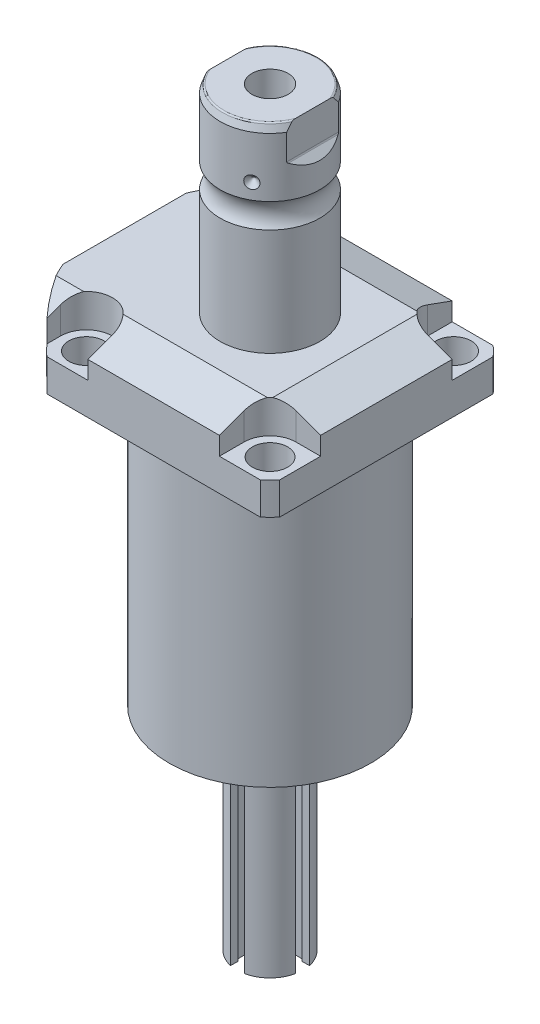
SolidWorks part; units mm, degrees
material "Alloy Steel"
ref_plane "Front Plane" through (0, 0, 0) normal (0, 0, 1) x (1, 0, 0)
ref_plane "Top Plane" through (0, 0, 0) normal (0, 1, 0) x (1, 0, 0)
ref_plane "Right Plane" through (0, 0, 0) normal (1, 0, 0) x (0, 0, -1)
ref_plane "Plane1" through (0, 0, 0) normal (0, 1, 0) x (0, 0, 1)
sketch "Sketch1" plane through (0, 0, 0) normal (0, 1, 0) x (0, 0, 1)
  line L0 (-44.45, 44.45) -> (44.45, 44.45)
  line L1 (44.45, 44.45) -> (44.45, -55.5498)
  line L2 (44.45, -55.5498) -> (-44.45, -55.5498)
  line L3 (-44.45, -55.5498) -> (-44.45, 44.45)
  line L4 (0, 0) -> (0, -60.6467) construction
  dimension "D1" = 55.5498
  dimension "D2" = 99.9998
  dimension "D3" = 88.9
extrude "Extrude1" add sketch "Sketch1" along normal blind 129.794
sketch "Sketch2" plane through (0, 0, 0) normal (0, -1, 0) x (1, 0, 0)
  circle A0 centre (0, 0) radius 60.325
  dimension "D1" = 120.65
extrude "Cut-Extrude1" cut sketch "Sketch2" against normal through all flip side to cut
ref_plane "Plane2" through (0, 0, 0) normal (1, 0, 0) x (0, 0, 1)
sketch "Sketch3" plane through (0, 0, 0) normal (1, 0, 0) x (0, 0, 1)
  line L0 (38.4937, 0) -> (38.4937, -104.775)
  line L1 (38.4937, -104.775) -> (76.5937, -104.775)
  line L2 (76.5937, -104.775) -> (76.5937, 0)
  line L3 (76.5937, 0) -> (38.4937, 0)
  line L4 (0, -93.345) -> (0, 4.445) construction
  line L5 (40.7836, 0) -> (-40.7836, 0) construction
  dimension "D1" = 76.9874
  dimension "D2" = 153.1874
  dimension "D3" = 104.775
revolve "Cut-Revolve1" cut sketch "Sketch3" angle 360 about L4
fillet "Fillet1" radius 0.381 1 edges at (0, 104.775, 38.4937)
sketch "Sketch4" plane through (0, 129.794, 0) normal (0, 1, 0) x (-1, 0, 0)
  line L0 (-44.45, 40.7836) -> (-44.45, -40.7836) construction
  line L1 (40.7836, 44.45) -> (-40.7836, 44.45) construction
  line L2 (-25.1206, -44.45) -> (-25.1206, -35.052)
  line L3 (-44.45, -44.45) -> (-25.1206, -44.45)
  line L4 (-44.45, -25.1206) -> (-44.45, -44.45)
  line L5 (-35.052, -25.1206) -> (-44.45, -25.1206)
  line L6 (44.9834, -44.45) -> (25.1206, -44.45)
  line L7 (25.1206, 44.45) -> (25.1206, 35.052)
  line L8 (44.9834, 44.45) -> (44.9834, 35.052)
  line L9 (44.9834, 44.45) -> (25.1206, 44.45)
  line L10 (-35.052, 25.1206) -> (-44.45, 25.1206)
  line L11 (-44.45, 25.1206) -> (-44.45, 44.45)
  line L12 (-44.45, 44.45) -> (-25.1206, 44.45)
  line L13 (-25.1206, 44.45) -> (-25.1206, 35.052)
  line L14 (-48.9217, 0) -> (49.4551, 0) construction
  line L15 (44.9834, -44.45) -> (44.9834, -35.052)
  line L16 (25.1206, -44.45) -> (25.1206, -35.052)
  arc A0 (25.1206, -35.052) -> (44.9834, -35.052) centre (35.052, -35.052) cw
  arc A1 (-35.052, -25.1206) -> (-25.1206, -35.052) centre (-35.052, -35.052) cw
  arc A2 (-35.052, 25.1206) -> (-25.1206, 35.052) centre (-35.052, 35.052) ccw
  arc A3 (25.1206, 35.052) -> (44.9834, 35.052) centre (35.052, 35.052) ccw
  dimension "D2" = 9.9314
  dimension "D1" = 35.052
  dimension "D3" = 35.052
  dimension "D4" = 35.052
extrude "Cut-Extrude2" cut sketch "Sketch4" against normal blind 12.7
ref_plane "Plane3" through (0, 0, 0) normal (1, 0, 0) x (0, 0, -1)
sketch "Sketch5" plane through (0, 0, 0) normal (1, 0, 0) x (0, 0, -1)
  line L0 (-28.575, 129.794) -> (-44.45, 124.016)
  line L1 (0, 0) -> (0, 154.1081) construction
  line L2 (-28.575, 129.794) -> (-44.45, 129.794)
  line L3 (-44.45, 129.794) -> (-44.45, 124.016)
  dimension "D1" = 15.875
  dimension "D2" = 20
extrude "Cut-Extrude9" cut sketch "Sketch5" against normal through all and the other way through all
mirror "Mirror1" about plane through (0, 0, 0) normal (0, 0, 1) of "Cut-Extrude9"
ref_plane "Plane7" through (0, 0, 0) normal (0, 0, 1) x (1, 0, 0)
sketch "Sketch9" plane through (0, 0, 0) normal (0, 0, 1) x (1, 0, 0)
  line L0 (28.575, 129.794) -> (44.45, 124.016)
  line L1 (44.45, 124.016) -> (44.45, 129.794)
  line L2 (44.45, 129.794) -> (28.575, 129.794)
  dimension "D1" = 15.875
  dimension "D2" = 20
extrude "Cut-Extrude7" cut sketch "Sketch9" against normal through all and the other way through all
ref_plane "Plane8" through (-41.402, 88.9, -18.1102) normal (1, 0, 0) x (0, 1, 0)
sketch "Sketch20" plane through (-41.402, 88.9, -18.1102) normal (1, 0, 0) x (0, 1, 0)
  line L0 (-88.9, 18.1102) -> (39.8401, 18.1102) construction
  line L1 (-7.2797, 36.2204) -> (36.9042, 36.2204) construction
  line L2 (15.875, 41.9227) -> (17.3228, 41.9227)
  line L3 (15.875, 58.8938) -> (15.875, -22.6734) construction
  line L4 (17.3228, 41.9227) -> (17.3228, 39.4716)
  line L5 (17.3228, 39.4716) -> (18.3388, 39.4716)
  line L6 (18.3388, 39.4716) -> (18.3388, 37.465)
  line L7 (18.3388, 37.465) -> (29.3116, 37.465)
  line L8 (29.3116, 37.465) -> (29.3116, 36.2204)
  line L9 (29.3116, 36.2204) -> (15.875, 36.2204)
  line L10 (15.875, 41.9227) -> (15.875, 36.2204)
  dimension "D1" = 18.1102
  dimension "D2" = 11.4046
  dimension "D3" = 1.4478
  dimension "D4" = 6.5024
  dimension "D5" = 1.016
  dimension "D6" = 2.4892
  dimension "D7" = 10.9728
revolve "Cut-Revolve4" cut sketch "Sketch20" angle 360 about L1
mirror "Mirror10" about plane through (0, 0, 0) normal (0, 0, 1) of "Cut-Revolve4"
sketch "Sketch10" plane through (-41.402, 88.9, -18.1102) normal (1, 0, 0) x (0, 1, 0)
  line L0 (-1.0325, 0) -> (1.5659, 0) construction
  line L1 (29.3116, 1.2446) -> (18.3388, 1.2446) construction
  line L2 (18.3388, -1.2446) -> (29.3116, -1.2446) construction
  line L3 (15.875, 58.8938) -> (15.875, -22.6734) construction
  circle A0 centre (16.1417, 4.5212) radius 1.1811
  dimension "D1" = 2.3622
  dimension "D2" = 0.2667
  dimension "D3" = 9.0424
revolve "Revolve4" add sketch "Sketch10" angle 360 about L0
ref_plane "Plane9" through (-41.402, 88.9, 18.1102) normal (1, 0, 0) x (0, 1, 0)
sketch "Sketch11" plane through (-41.402, 88.9, 18.1102) normal (1, 0, 0) x (0, 1, 0)
  line L0 (-1.0325, 0) -> (1.5659, 0) construction
  line L1 (29.3116, 1.2446) -> (18.3388, 1.2446) construction
  line L3 (15.875, 22.6734) -> (15.875, -58.8938) construction
  line L4 (18.3388, -1.2446) -> (29.3116, -1.2446) construction
  circle A0 centre (16.1417, 4.5212) radius 1.1811
  dimension "D1" = 2.3622
  dimension "D2" = 9.0424
  dimension "D3" = 0.2667
revolve "Revolve2" add sketch "Sketch11" angle 360 about L0
ref_plane "Plane10" through (-55.5498, 101.9048, 12.9794) normal (0, 0, 1) x (0, 1, 0)
sketch "S2D0007" plane through (-55.5498, 101.9048, 12.9794) normal (0, 0, 1) x (0, 1, 0)
  line L0 (15.875, 0) -> (26.3525, 0)
  line L1 (26.3525, 0) -> (26.3525, -0.254)
  line L2 (26.3525, -0.254) -> (22.0599, -0.254)
  line L3 (22.0599, -0.254) -> (21.5173, -2.8067)
  line L4 (21.5173, -2.8067) -> (20.8534, -3.4706)
  line L5 (20.8534, -3.4706) -> (20.8534, -14.224)
  line L6 (20.8534, -14.224) -> (15.875, -14.224)
  line L7 (15.875, -14.224) -> (15.875, 0)
  line L8 (15.875, -1000) -> (15.875, 49000) construction
  line L9 (2.8702, 0) -> (2.8702, -14.7662) construction
  dimension "D1" = 0.254
  dimension "D2" = 13.0048
  dimension "D3" = 9.9568
  dimension "D4" = 20.955
  dimension "D5" = 12.3698
  dimension "D6" = 12
  dimension "D7" = 45
  dimension "D8" = 13.97
  dimension "D9" = 2.5527
revolve "Cut-Revolve2" cut sketch "S2D0007" angle 360 about L8
ref_plane "Plane11" through (-55.5498, 101.9048, -12.9794) normal (0, 0, 1) x (0, 1, 0)
sketch "Sketch13" plane through (-55.5498, 101.9048, -12.9794) normal (0, 0, 1) x (0, 1, 0)
  line L0 (15.875, 0) -> (26.3525, 0)
  line L1 (26.3525, 0) -> (26.3525, -0.254)
  line L2 (26.3525, -0.254) -> (22.0599, -0.254)
  line L3 (22.0599, -0.254) -> (21.5173, -2.8067)
  line L4 (21.5173, -2.8067) -> (20.8534, -3.4706)
  line L5 (20.8534, -3.4706) -> (20.8534, -14.224)
  line L6 (20.8534, -14.224) -> (15.875, -14.224)
  line L7 (15.875, -14.224) -> (15.875, 0)
  line L8 (15.875, -1000) -> (15.875, 49000) construction
  line L9 (2.8702, 0) -> (2.8702, -14.7662) construction
  dimension "D1" = 0.254
  dimension "D2" = 13.0048
  dimension "D3" = 20.955
  dimension "D4" = 12.3698
  dimension "D5" = 12
  dimension "D6" = 45
  dimension "D7" = 2.5527
  dimension "D8" = 13.97
  dimension "D9" = 9.9568
revolve "Cut-Revolve3" cut sketch "Sketch13" angle 360 about L8
ref_plane "Plane12" through (0, 0, 0) normal (1, 0, 0) x (0, -1, 0)
sketch "Sketch15" plane through (0, 0, 0) normal (1, 0, 0) x (0, -1, 0)
  line L0 (-129.794, 0) -> (-129.794, 19.05)
  line L1 (-129.794, 19.05) -> (-170.5783, 19.05)
  line L2 (-179.9925, 19.05) -> (-202.5396, 19.05)
  line L3 (-205.4606, 17.9868) -> (-205.4606, 0)
  line L4 (-205.4606, 0) -> (-129.794, 0)
  line L5 (-197.6361, 0) -> (-64.6704, 0) construction
  line L6 (-129.794, 27.5233) -> (-129.794, -27.5233) construction
  line L7 (-104.775, 40.7836) -> (-104.775, 44.45) construction
  line L8 (-205.4606, 17.9868) -> (-202.5396, 19.05)
  arc A0 (-179.9925, 19.05) -> (-170.5783, 19.05) centre (-175.2854, 25.4254) ccw
  dimension "D2" = 20
  dimension "D4" = 7.9248
  dimension "D6" = 35.0012
  dimension "D1" = 100.6856
  dimension "D3" = 38.1
  dimension "D5" = 30.1752
  dimension "D7" = 2.921
revolve "Revolve3" add sketch "Sketch15" angle 360 about L5
ref_plane "Plane13" through (0, 0, 0) normal (0, 0, -1) x (0, -1, 0)
sketch "Sketch16" plane through (0, 0, 0) normal (0, 0, -1) x (0, -1, 0)
  line L0 (-205.4606, 19.05) -> (-189.6764, 19.05)
  line L1 (-205.4606, -19.05) -> (-205.4606, -16.2814)
  line L2 (-205.4606, 16.2814) -> (-192.7606, 16.2814)
  line L3 (-192.2218, 16.5046) -> (-189.6764, 19.05)
  line L4 (-192.2218, -16.5046) -> (-189.6764, -19.05)
  line L5 (-205.4606, -16.2814) -> (-192.7606, -16.2814)
  line L6 (-205.4606, 19.05) -> (-205.4606, 16.2814)
  line L7 (-205.4606, -19.05) -> (-189.6764, -19.05)
  line L8 (-194.0458, 0) -> (-125.0021, 0) construction
  line L11 (-205.4606, 17.9868) -> (-205.4606, -17.9868) construction
  line L12 (-179.9925, 19.05) -> (-202.5396, 19.05) construction
  arc A0 (-192.7606, 16.2814) -> (-192.2218, 16.5046) centre (-192.7606, 17.0434) ccw
  arc A1 (-192.7606, -16.2814) -> (-192.2218, -16.5046) centre (-192.7606, -17.0434) cw
  point P3 (-192.445, 16.2814)
  dimension "D4" = 0.762
  dimension "D1" = 32.5628
  dimension "D2" = 45
  dimension "D3" = 12.7
extrude "Cut-Extrude8" cut sketch "Sketch16" against normal mid plane 106.68
hole_wizard "Hole1" positions "Sketch18" profile "Sketch17" legacy end condition up to next
sketch "Sketch18" plane through (0, 117.094, 0) normal (0, 1, 0) x (-1, 0, 0)
  arc A0 (44.9834, -35.052) -> (25.1206, -35.052) centre (35.052, -35.052) ccw construction
  arc A1 (25.1206, 35.052) -> (44.9834, 35.052) centre (35.052, 35.052) ccw construction
  arc A2 (-35.052, 25.1206) -> (-25.1206, 35.052) centre (-35.052, 35.052) ccw construction
  arc A3 (-25.1206, -35.052) -> (-35.052, -25.1206) centre (-35.052, -35.052) ccw construction
  point P0 (-35.052, -35.052)
  point P1 (-35.052, 35.052)
  point P3 (35.052, 35.052)
  point P5 (35.052, -35.052)
sketch "Sketch17" plane through (35.052, 117.094, -35.052) normal (1, 0, 0) x (0, 0, 1)
  line L0 (0, 0) -> (0, 12.319)
  line L1 (0, 12.319) -> (6.7437, 12.319)
  line L2 (6.7437, 12.319) -> (6.7437, 0)
  line L3 (6.7437, 0) -> (0, 0)
  line L4 (0, 110) -> (0, -10) construction
  dimension "Diameter" = 13.4874
  dimension "Depth" = 12.319
chamfer "Chamfer1" distance 0.635 angle 45 2 edges at (-41.402, 107.2388, 16.8656) (-41.402, 107.2388, -16.8656)
sketch "Sketch21" plane through (0, 0, 0) normal (0, 0, 1) x (1, 0, 0)
  line L0 (0, 0) -> (0, 194.0957) construction
  line L1 (0, 180.0606) -> (6.9342, 184.2271)
  line L2 (6.9342, 184.2271) -> (6.9342, 205.4606)
  line L4 (6.9342, 205.4606) -> (0, 205.4606)
  line L5 (0, 205.4606) -> (0, 180.0606)
  line L6 (16.2814, 205.4606) -> (-16.2814, 205.4606) construction
  dimension "D1" = 13.8684
  dimension "D2" = 59
  dimension "D3" = 25.4
revolve "Cut-Revolve5" cut sketch "Sketch21" angle 360 about L0
fillet "Fillet2" radius 0.635 2 edges at (0, 205.4606, 17.9868) (0, 205.4606, -17.9868)
sketch "Sketch22" plane through (0, 0, 0) normal (0, 0, 1) x (1, 0, 0)
  line L0 (-37.9974, 185.9534) -> (37.12, 185.9534) construction
  line L1 (-19.05, 188.3664) -> (-16.637, 185.9534)
  line L2 (-16.637, 185.9534) -> (-19.05, 185.9534)
  line L3 (-19.05, 185.9534) -> (-19.05, 188.3664)
  line L4 (-19.05, 189.6764) -> (-19.05, 179.9925) construction
  arc A0 (-19.05, 170.5783) -> (-19.05, 179.9925) centre (-25.4254, 175.2854) ccw construction
  dimension "D2" = 10.668
  dimension "D1" = 4.826
  dimension "D3" = 45
revolve "Cut-Revolve6" cut sketch "Sketch22" angle 360 about L0
pattern_circular "CirPattern1" count 3 over 360 about axis through (0, 197.6361, 0) along (0, 1, 0) of "Cut-Revolve6"
sketch "Sketch23" plane through (0, 0, 0) normal (0, 0, 1) x (1, 0, 0)
  line L0 (0, -1000) -> (0, 49000) construction
  line L1 (0, 0) -> (22.225, 0)
  line L2 (-38.4937, 0) -> (38.4937, 0) construction
  line L3 (22.225, 0) -> (22.225, -2.54)
  line L4 (22.225, -2.54) -> (12.7, -2.54)
  line L5 (12.7, -2.54) -> (12.7, -81.28)
  line L6 (12.7, -81.28) -> (0, -81.28)
  line L7 (0, -81.28) -> (0, 0)
  dimension "D1" = 44.45
  dimension "D2" = 25.4
  dimension "D3" = 2.54
  dimension "D4" = 81.28
revolve "Revolve5" add sketch "Sketch23" angle 360 about L0
sketch "Sketch24" plane through (0, -2.54, 0) normal (0, -1, 0) x (1, 0, 0)
  line L0 (-1000, 0) -> (49000, 0) construction
  line L1 (0, -1000) -> (0, 49000) construction
  line L2 (0, 0) -> (43301.2702, 25000) construction
  line L3 (0, 0) -> (25000, 43301.2702) construction
  circle A0 centre (0, 0) radius 19.431 construction
  circle A1 centre (19.431, 0) radius 1.7272
  circle A2 centre (16.8277, 9.7155) radius 1.7272
  circle A3 centre (9.7155, 16.8277) radius 1.7272
  circle A4 centre (0, 19.431) radius 1.7272
  circle A5 centre (-9.7155, 16.8277) radius 1.7272
  circle A6 centre (-16.8277, 9.7155) radius 1.7272
  circle A7 centre (-19.431, 0) radius 1.7272
  circle A8 centre (-16.8277, -9.7155) radius 1.7272
  circle A9 centre (-9.7155, -16.8277) radius 1.7272
  circle A10 centre (0, -19.431) radius 1.7272
  circle A11 centre (9.7155, -16.8277) radius 1.7272
  circle A12 centre (16.8277, -9.7155) radius 1.7272
  dimension "D3" = 38.862
  dimension "D4" = 3.4544
  dimension "D5" = 3.4544
  dimension "D6" = 3.4544
  dimension "D7" = 3.4544
  dimension "D1" = 30
  dimension "D2" = 30
extrude "Cut-Extrude10" cut sketch "Sketch24" against normal up to surface (2.54 mm away) up to face at (0, 0, -22.225)
sketch "Sketch25" plane through (0, -2.54, 0) normal (0, -1, 0) x (1, 0, 0)
  circle A0 centre (19.431, 0) radius 2.7051
  circle A1 centre (-9.7155, 16.8277) radius 2.7051
  circle A2 centre (-9.7155, -16.8277) radius 2.7051
  dimension "D1" = 5.4102
  dimension "D2" = 5.4102
  dimension "D3" = 5.4102
extrude "Extrude2" add sketch "Sketch25" along normal blind 2.9464
ref_plane "Plane15-slot-angle" through (0, 0, 0) normal (1, 0, 0) x (0, 0, -1)
ref_plane "Plane16" through (0, -41.91, 12.7) normal (0, 0, 1) x (-1, 0, 0)
sketch "Sketch31" plane through (0, -41.91, 12.7) normal (0, 0, 1) x (-1, 0, 0)
  line L0 (0, -1034.036) -> (0, 48965.964) construction
  line L1 (0, -1034.036) -> (0, 48965.964) construction
  line L2 (-2.6416, -28.9574) -> (-2.6416, 39.37)
  line L3 (12.7, 39.37) -> (-12.7, 39.37) construction
  line L4 (-2.6416, 39.37) -> (2.6416, 39.37)
  line L5 (2.6416, -28.9574) -> (2.6416, 39.37)
  arc A0 (-2.6416, -28.9574) -> (2.6416, -28.9574) centre (0, -31.242) ccw
  point P14 (0, 39.37)
  dimension "D1" = 6.985
  dimension "D2" = 5.2832
  dimension "D3" = 70.612
extrude "Cut-Extrude11" cut sketch "Sketch31" against normal blind 6.477
sketch "Sketch32" plane through (0, 0, 6.223) normal (0, 0, 1) x (1, 0, 0)
  line L0 (0, -1000) -> (0, 49000) construction
  line L1 (3.4925, -10.668) -> (3.4925, -81.28)
  line L2 (-12.7, -81.28) -> (12.7, -81.28) construction
  line L3 (3.4925, -81.28) -> (-3.4925, -81.28)
  line L4 (-2.6416, -81.28) -> (2.6416, -81.28) construction
  line L5 (3.4925, -10.668) -> (-3.4925, -10.668)
  line L6 (-3.4925, -10.668) -> (-3.4925, -81.28)
  point P13 (0, -81.28)
  point P14 (0, -10.668)
  dimension "D1" = 6.985
extrude "Cut-Extrude12" cut sketch "Sketch32" along normal blind 3.302
ref_plane "Plane17" through (0, 0, 0) normal (0, 0, 1) x (1, 0, 0)
mirror "Mirror11" about plane through (0, 0, 0) normal (0, 0, 1) of "Cut-Extrude12", "Cut-Extrude11"
sketch "Sketch35" plane through (0, -5.4864, 0) normal (0, -1, 0) x (1, 0, 0)
  line L1 (19.431, -1.4371) -> (20.6756, -0.7186)
  line L2 (20.6756, -0.7186) -> (20.6756, 0.7186)
  line L3 (20.6756, 0.7186) -> (19.431, 1.4371)
  line L4 (19.431, 1.4371) -> (18.1864, 0.7186)
  line L5 (18.1864, 0.7186) -> (18.1864, -0.7186)
  line L6 (18.1864, -0.7186) -> (19.431, -1.4371)
  line L7 (-9.2553, 15.4663) -> (-8.3063, 16.5455)
  line L8 (-8.3063, 16.5455) -> (-8.7665, 17.907)
  line L9 (-8.7665, 17.907) -> (-10.1757, 18.1892)
  line L10 (-10.1757, 18.1892) -> (-11.1247, 17.1099)
  line L11 (-11.1247, 17.1099) -> (-10.6645, 15.7485)
  line L12 (-10.6645, 15.7485) -> (-9.2553, 15.4663)
  line L13 (-9.7155, -18.2649) -> (-8.4709, -17.5463)
  line L14 (-8.4709, -17.5463) -> (-8.4709, -16.1092)
  line L15 (-8.4709, -16.1092) -> (-9.7155, -15.3906)
  line L16 (-9.7155, -15.3906) -> (-10.9601, -16.1092)
  line L17 (-10.9601, -16.1092) -> (-10.9601, -17.5463)
  line L18 (-10.9601, -17.5463) -> (-9.7155, -18.2649)
  circle A0 centre (19.431, 0) radius 1.2446 construction
  circle A1 centre (-9.7155, 16.8277) radius 1.2446 construction
  circle A2 centre (-9.7155, -16.8277) radius 1.2446 construction
  dimension "D1" = 2.4892
  dimension "D2" = 2.4892
  dimension "D3" = 2.4892
extrude "Cut-Extrude13" cut sketch "Sketch35" against normal blind 2.032
pattern_circular "CirPattern2" count 2 every 90 about axis through (0, 0, 0) along (0, 1, 0) of "Mirror11", "Cut-Extrude11", "Cut-Extrude12"
